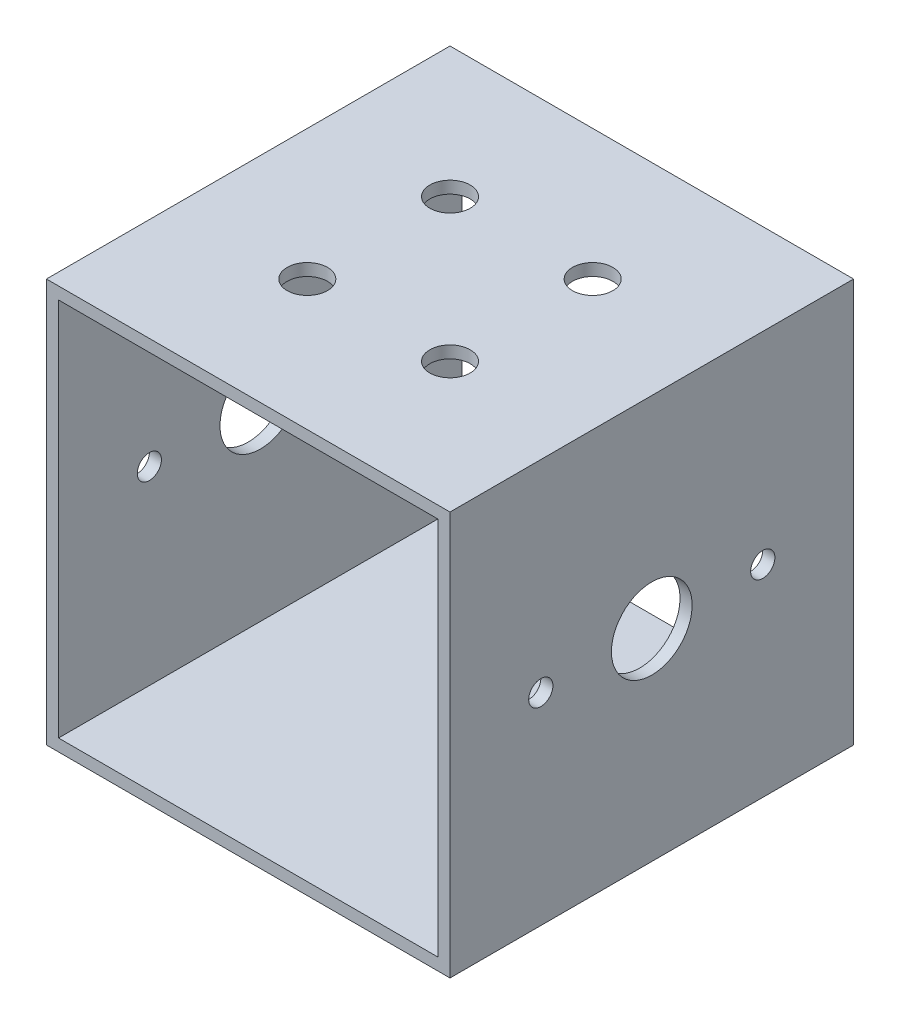
SolidWorks part; units mm, degrees
material "Liga 1060"
ref_plane "Plano frontal" through (0, 0, 0) normal (0, 0, 1) x (1, 0, 0)
ref_plane "Plano superior" through (0, 0, 0) normal (0, 1, 0) x (1, 0, 0)
ref_plane "Plano direito" through (0, 0, 0) normal (1, 0, 0) x (0, 0, -1)
sketch "Esboço1" plane through (0, 0, 0) normal (0, 0, 1) x (1, 0, 0)
  line L0 (25, -25) -> (25, 25)
  line L1 (23.5, -23.5) -> (-23.5, -23.5)
  line L2 (23.5, -23.5) -> (23.5, 23.5)
  line L3 (23.5, 23.5) -> (-23.5, 23.5)
  line L4 (-23.5, -23.5) -> (-23.5, 23.5)
  line L5 (23.5, -23.5) -> (-23.5, 23.5) construction
  line L6 (23.5, 23.5) -> (-23.5, -23.5) construction
  line L7 (25, 25) -> (-25, 25)
  line L8 (-25, -25) -> (-25, 25)
  line L9 (25, -25) -> (-25, -25)
  point P0 (0, 0)
  dimension "D1" = 50
  dimension "D2" = 50
  dimension "D3" = 47
extrude "Ressalto-extrusão1" add sketch "Esboço1" along normal blind 50
sketch "Esboço2" plane through (0, 25, 0) normal (0, 1, 0) x (1, 0, 0)
  line L0 (-25, -25) -> (25, -25) construction
  line L1 (-25, -50) -> (-25, 0) construction
  line L2 (25, -50) -> (25, 0) construction
  line L3 (0, 0) -> (0, -50) construction
  line L4 (25, 0) -> (-25, 0) construction
  line L5 (25, -50) -> (-25, -50) construction
  line L6 (0, -25) -> (17.6777, -7.3223) construction
  circle A0 centre (0, -25) radius 25
  circle A1 centre (8.8388, -16.1612) radius 2.5
  circle A2 centre (-8.8388, -16.1612) radius 2.5
  circle A3 centre (8.8388, -33.8388) radius 2.5
  circle A4 centre (-8.8388, -33.8388) radius 2.5
  dimension "D1" = 50
  dimension "D2" = 5
sketch "Esboço3" plane through (25, 0, 0) normal (1, 0, 0) x (0, 0, -1)
  line L0 (-25, 25) -> (-25, -25) construction
  line L1 (-50, 25) -> (0, 25) construction
  line L2 (-50, -25) -> (0, -25) construction
  line L3 (-50, 0) -> (0, 0) construction
  line L4 (-50, -25) -> (-50, 25) construction
  line L5 (0, -25) -> (0, 25) construction
  circle A0 centre (-25, 0) radius 5
  dimension "D1" = 10
extrude "Corte-extrusão1" cut sketch "Esboço3" against normal through all and the other way through all
extrude "Corte-extrusão2" cut sketch "Esboço2" against normal blind 10 contours A2 | A1 | A4 | A3
sketch "Esboço4" plane through (25, 0, 0) normal (1, 0, 0) x (0, 0, -1)
  circle A0 centre (-11.25, 0) radius 2.5 construction
  circle A1 centre (-38.75, 0) radius 2.5 construction
  circle A2 centre (-11.25, 0) radius 2.5
  circle A3 centre (-38.75, 0) radius 2.5
sketch "Esboço5" plane through (25, 0, 0) normal (1, 0, 0) x (0, 0, -1)
  circle A0 centre (-11.25, 0) radius 1.5
  circle A1 centre (-38.75, 0) radius 1.5
  dimension "D1" = 3
  dimension "D2" = 3
extrude "Corte-extrusão3" cut sketch "Esboço5" against normal through all and the other way through all
